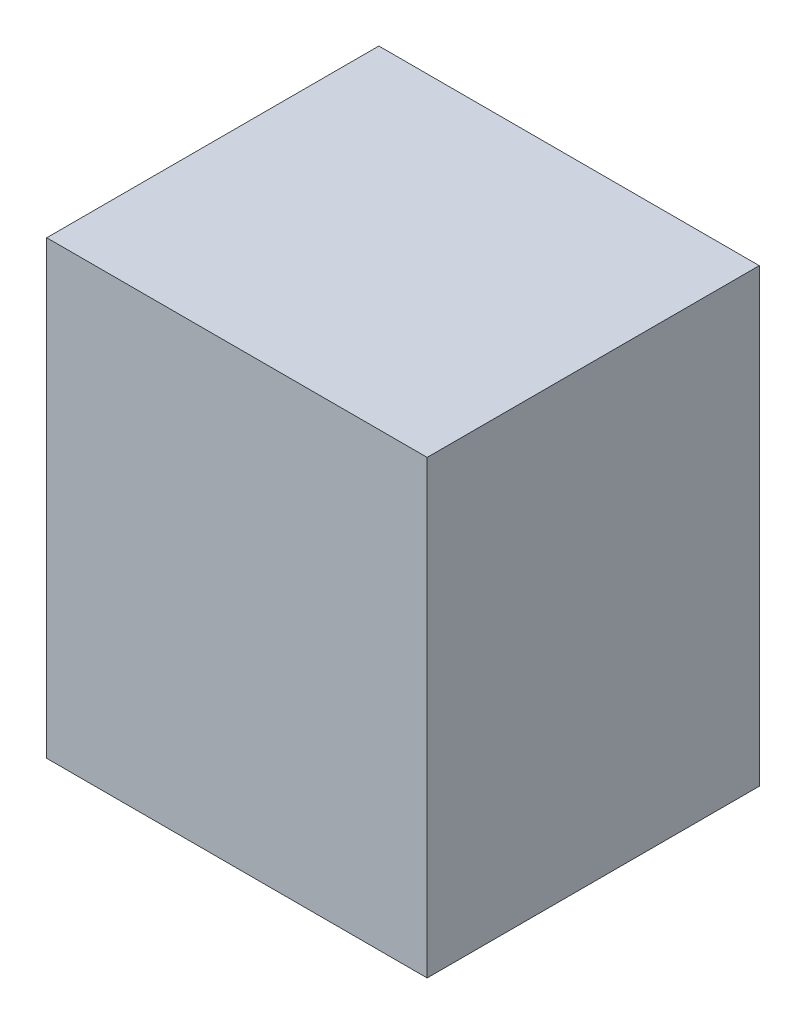
SolidWorks part; units mm, degrees
ref_plane "Front Plane" through (0, 0, 0) normal (0, 0, 1) x (1, 0, 0)
ref_plane "Top Plane" through (0, 0, 0) normal (0, 1, 0) x (1, 0, 0)
ref_plane "Right Plane" through (0, 0, 0) normal (1, 0, 0) x (0, 0, -1)
sketch "Sketch1" plane through (0, 0, 0) normal (0, 1, 0) x (1, 0, 0)
  line L1 (0, 0) -> (480.06, 0)
  line L2 (0, 0) -> (0, -419.1)
  line L3 (0, -419.1) -> (480.06, -419.1)
  line L4 (480.06, 0) -> (480.06, -419.1)
extrude "Boss-Extrude1" add sketch "Sketch1" along normal blind 568.96
